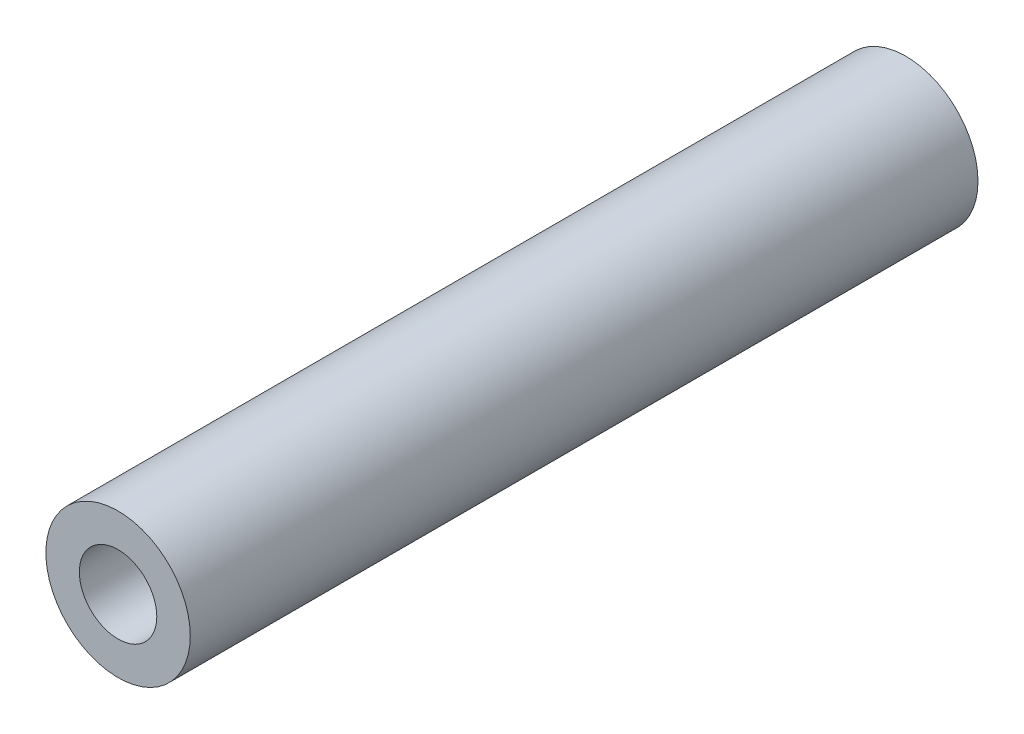
SolidWorks part; units mm, degrees
ref_plane "Alzado" through (0, 0, 0) normal (0, 0, 1) x (1, 0, 0)
ref_plane "Planta" through (0, 0, 0) normal (0, 1, 0) x (1, 0, 0)
ref_plane "Vista lateral" through (0, 0, 0) normal (1, 0, 0) x (0, 0, -1)
sketch "Croquis1" plane through (0, 0, 0) normal (0, 0, 1) x (1, 0, 0)
  circle A0 centre (0, 0) radius 5.5
  dimension "D1" = 11
extrude "Saliente-Extruir1" add sketch "Croquis1" along normal blind 60
hole_wizard "Taladro roscado M5x0.81" [suppressed] positions "Croquis3" profile "Croquis4" tap size "M5x0.8" standard "Ansi Metric"
sketch "Croquis3" plane through (0, 0, 0) normal (0, 0, -1) x (-1, 0, 0)
  point P0 (0, 0)
sketch "Croquis4" plane through (0, 0, 0) normal (1, 0, 0) x (0, 1, 0)
  line L0 (0, 0) -> (0, 10)
  line L1 (0, 10) -> (2.1, 8.7382)
  line L2 (2.1, 8.7382) -> (2.1, 0.675)
  line L3 (2.1, 0.675) -> (2.775, 0)
  line L5 (2.775, 0) -> (0, 0)
  line L6 (-2.1, 0.675) -> (-2.775, 0) construction
  line L10 (0, 10) -> (-2.1, 8.7382) construction
  line L11 (0, -6.35) -> (0, 107.95) construction
  dimension "Diámetro de perforador para roscar" = 4.2
  dimension "Profundidad de perforador para roscar" = 10
  dimension "Diámetro de avellanado cercano" = 5.55
  dimension "Ángulo de avellanado cercano" = 90
  dimension "Ángulo de perforador" = 118
cosmetic thread "Rosca de taladro1" [suppressed] parameters "D1"=10, "D2"=5
sketch "Croquis2" plane through (0, 0, 0) normal (0, 0, 1) x (1, 0, 0)
  circle A0 centre (0, 0) radius 2.95
  dimension "D1" = 5.9
extrude "Cortar-Extruir1" [suppressed] cut sketch "Croquis2" along normal blind 10
sketch "Croquis5" plane through (0, 0, 0) normal (0, 0, -1) x (-1, 0, 0)
  circle A0 centre (0, 0) radius 1.775
  dimension "D1" = 3.55
extrude "Saliente-Extruir2" [suppressed] add sketch "Croquis5" along normal blind 20
sketch "Croquis6" plane through (0, 0, 60) normal (0, 0, 1) x (1, 0, 0)
  circle A0 centre (0, 0) radius 2.95
  dimension "D1" = 5.9
extrude "Cortar-Extruir2" cut sketch "Croquis6" against normal blind 15
sketch "Croquis9" plane through (0, 0, 0) normal (0, 0, -1) x (-1, 0, 0)
  circle A0 centre (0, 0) radius 2.025
  dimension "D1" = 4.05
extrude "Cortar-Extruir6" cut sketch "Croquis9" against normal through all
ref_plane "Plano1" through (5.5, 0, 0) normal (1, 0, 0) x (0, 0, -1)
sketch "Croquis10" plane through (5.5, -3.9, 0) normal (-1, 0, 0) x (0, 1, 0)
  circle A0 centre (3.9, -10) radius 2.925
  dimension "D1" = 5.85
  dimension "D2" = 10
extrude "Cortar-Extruir7" [suppressed] cut sketch "Croquis10" along normal mid plane 10
